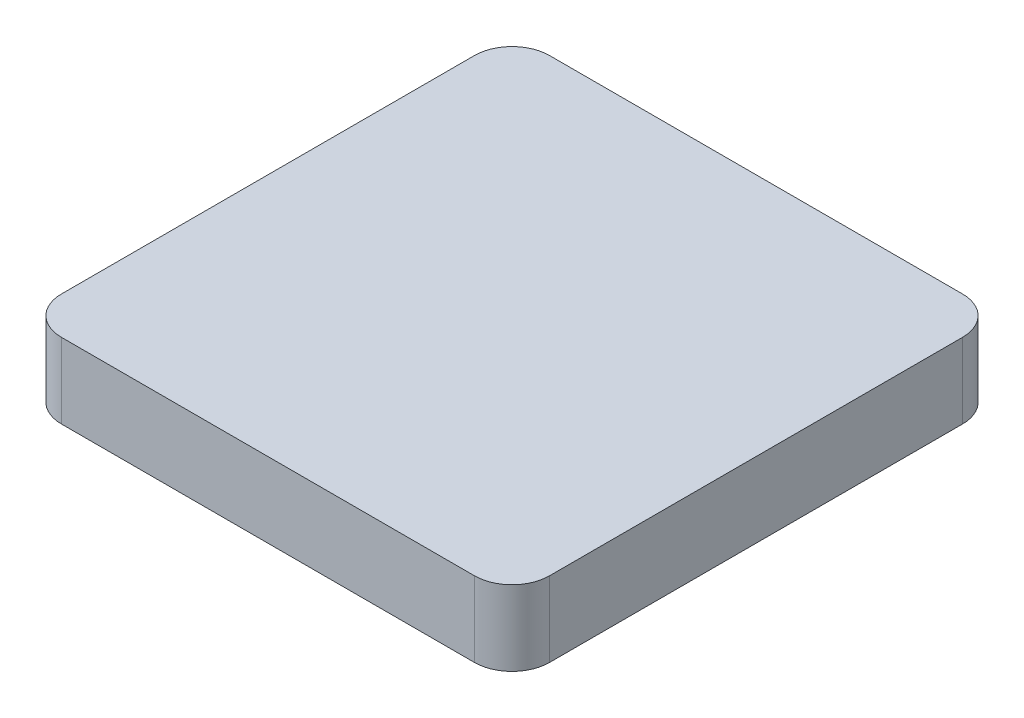
SolidWorks part; units mm, degrees
material "aluminio"
ref_plane "Alzado" through (0, 0, 0) normal (0, 0, 1) x (1, 0, 0)
ref_plane "Planta" through (0, 0, 0) normal (0, 1, 0) x (1, 0, 0)
ref_plane "Vista lateral" through (0, 0, 0) normal (1, 0, 0) x (0, 0, -1)
sketch "Sketch1" plane through (0, 0, 0) normal (0, 1, 0) x (1, 0, 0)
  line L1 (5.5, -6.5) -> (-5.5, -6.5)
  line L2 (6.5, -5.5) -> (6.5, 5.5)
  line L3 (5.5, 6.5) -> (-5.5, 6.5)
  line L4 (-6.5, -5.5) -> (-6.5, 5.5)
  line L5 (6.5, -6.5) -> (-6.5, 6.5) construction
  line L6 (6.5, 6.5) -> (-6.5, -6.5) construction
  arc A0 (6.5, -5.5) -> (5.5, -6.5) centre (5.5, -5.5) cw
  arc A1 (-5.5, -6.5) -> (-6.5, -5.5) centre (-5.5, -5.5) cw
  arc A2 (-5.5, 6.5) -> (-6.5, 5.5) centre (-5.5, 5.5) ccw
  arc A3 (6.5, 5.5) -> (5.5, 6.5) centre (5.5, 5.5) ccw
  point P0 (0, 0)
  dimension "D4" = 1
  dimension "D1" = 13
  dimension "D2" = 13
extrude "Boss-Extrude1" add sketch "Sketch1" along normal blind 2
